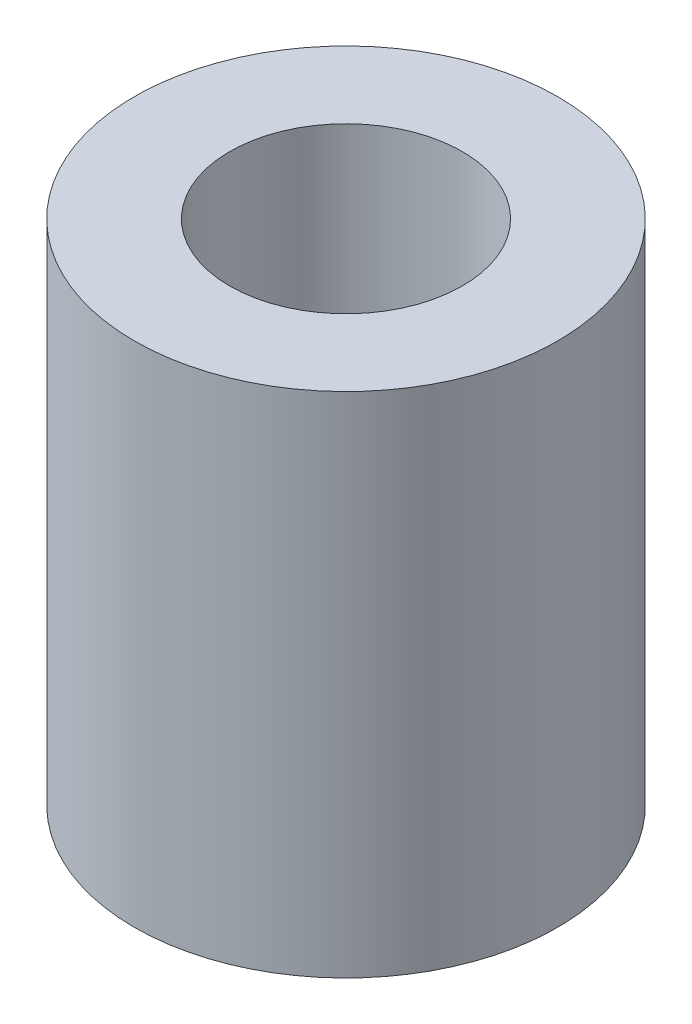
SolidWorks part; units mm, degrees
ref_plane "Plan de face" through (0, 0, 0) normal (0, 0, 1) x (1, 0, 0)
ref_plane "Plan de dessus" through (0, 0, 0) normal (0, 1, 0) x (1, 0, 0)
ref_plane "Plan de droite" through (0, 0, 0) normal (1, 0, 0) x (0, 0, -1)
sketch "Esquisse1" plane through (0, 0, 0) normal (0, 1, 0) x (1, 0, 0)
  circle A0 centre (0, 0) radius 5
  dimension "D1" = 10
extrude "Extrusion1" add sketch "Esquisse1" along normal blind 12
sketch "Esquisse2" plane through (0, 12, 0) normal (0, 1, 0) x (1, 0, 0)
  circle A0 centre (0, 0) radius 2.75
  dimension "D1" = 5.5
extrude "Enlèv. mat.-Extru.1" cut sketch "Esquisse2" against normal through all
